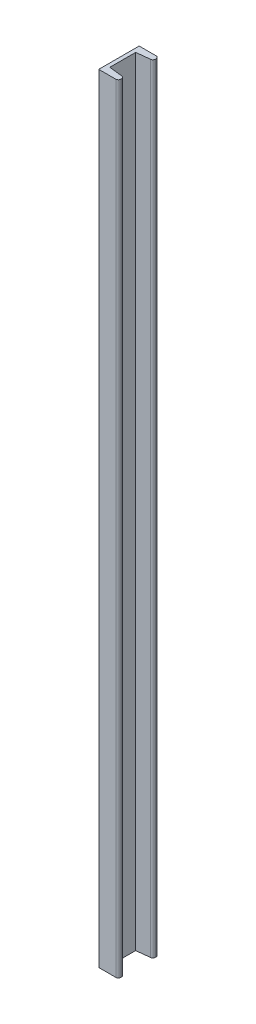
SolidWorks part; units mm, degrees
ref_plane "Plan de face" through (0, 0, 0) normal (0, 0, 1) x (1, 0, 0)
ref_plane "Plan de dessus" through (0, 0, 0) normal (0, 1, 0) x (1, 0, 0)
ref_plane "Plan de droite" through (0, 0, 0) normal (1, 0, 0) x (0, 0, -1)
sketch "Esquisse1" plane through (0, 0, 0) normal (0, 1, 0) x (1, 0, 0)
  line L0 (0, -3.7529) -> (0, 13.2722) construction
  line L1 (-1.2413, 0) -> (11.484, 0) construction
  line L2 (-1.2413, 8.05) -> (11.484, 8.05) construction
  line L3 (3.9, -3.7529) -> (3.9, 13.2722) construction
  line L4 (0.75, 13.2722) -> (0.75, -1.2855) construction
  line L5 (-0.6862, 6.6) -> (1.2569, 6.6) construction
  line L6 (3.5701, 6.95) -> (5.4207, 6.95) construction
  line L7 (2.7991, 4.025) -> (7.1787, 4.025) construction
  line L8 (0.75, 6.6) -> (3.4552, 6.9006)
  line L9 (3.9, 7.3975) -> (3.9, 7.55)
  line L10 (3.4, 8.05) -> (0, 8.05)
  line L11 (3.4, 0) -> (0, 0)
  line L12 (3.9, 0.6525) -> (3.9, 0.5)
  line L13 (0.75, 1.45) -> (3.4552, 1.1494)
  line L14 (0.75, 6.6) -> (0.75, 1.45)
  line L15 (0, 0) -> (0, 8.05)
  arc A0 (3.4552, 6.9006) -> (3.9, 7.3975) centre (3.4, 7.3975) ccw
  arc A1 (3.9, 7.55) -> (3.4, 8.05) centre (3.4, 7.55) ccw
  arc A2 (3.9, 0.5) -> (3.4, 0) centre (3.4, 0.5) cw
  arc A3 (3.4552, 1.1494) -> (3.9, 0.6525) centre (3.4, 0.6525) cw
  point P23 (3.9, 6.95)
  point P26 (3.9, 8.05)
  point P35 (3.9, 0)
  point P36 (3.9, 1.1)
  dimension "D7" = 0.5
  dimension "D1" = 8.05
  dimension "D2" = 3.9
  dimension "D3" = 0.75
  dimension "D4" = 1.45
  dimension "D5" = 1.1
  dimension "D6" = 4.025
extrude "Boss.-Extru.1" add sketch "Esquisse1" along normal blind 155
